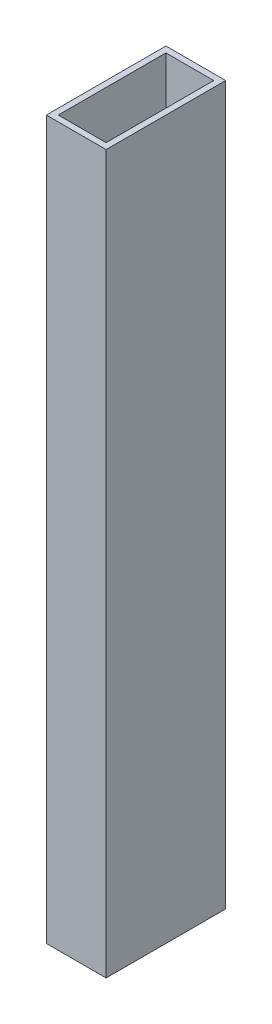
SolidWorks part; units mm, degrees
ref_plane "Спереди" through (0, 0, 0) normal (0, 0, 1) x (1, 0, 0)
ref_plane "Сверху" through (0, 0, 0) normal (0, 1, 0) x (1, 0, 0)
ref_plane "Справа" through (0, 0, 0) normal (1, 0, 0) x (0, 0, -1)
sketch "Sketch1" plane through (0, 0, 0) normal (0, 1, 0) x (1, 0, 0)
  line L1 (5, -10) -> (-5, -10)
  line L2 (5, -10) -> (5, 10)
  line L3 (5, 10) -> (-5, 10)
  line L4 (-5, -10) -> (-5, 10)
  line L5 (5, -10) -> (-5, 10) construction
  line L6 (5, 10) -> (-5, -10) construction
  line L7 (4, -9) -> (-4, -9)
  line L8 (4, -9) -> (4, 9)
  line L9 (4, 9) -> (-4, 9)
  line L10 (-4, -9) -> (-4, 9)
  line L11 (4, -9) -> (-4, 9) construction
  line L12 (4, 9) -> (-4, -9) construction
  point P0 (0, 0)
  point P6 (0, 0)
  dimension "D1" = 10
  dimension "D2" = 20
  dimension "D3" = 1
  dimension "D4" = 1
extrude "Boss-Extrude1" add sketch "Sketch1" along normal blind 120
